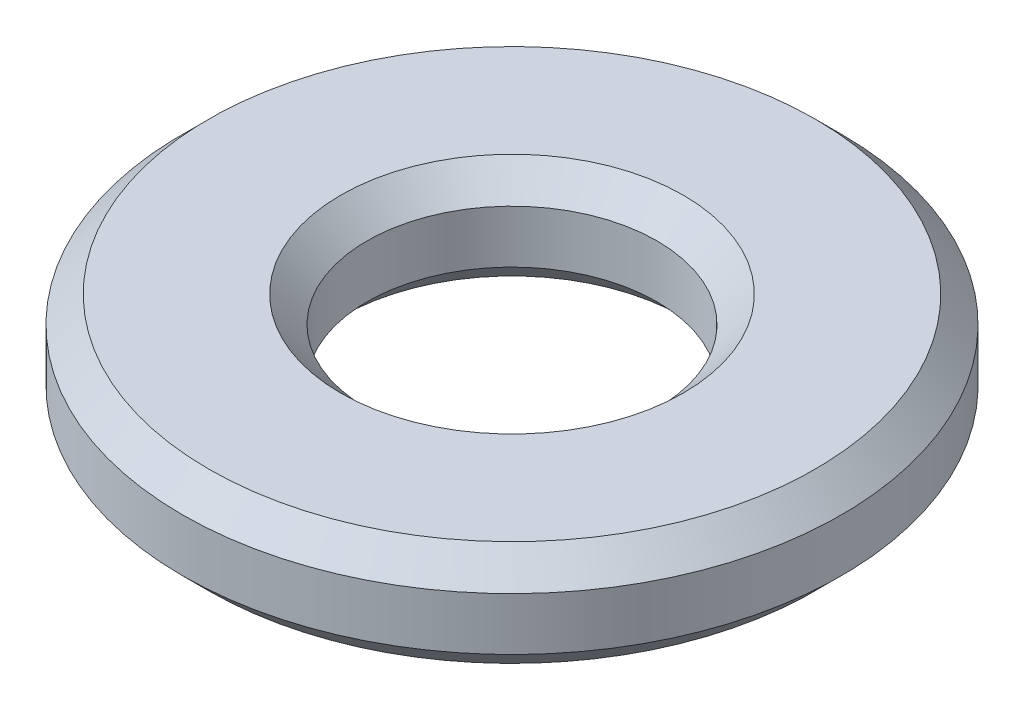
SolidWorks part; units mm, degrees
ref_plane "Alzado" through (0, 0, 0) normal (0, 0, 1) x (1, 0, 0)
ref_plane "Planta" through (0, 0, 0) normal (0, 1, 0) x (1, 0, 0)
ref_plane "Vista lateral" through (0, 0, 0) normal (1, 0, 0) x (0, 0, -1)
sketch "Croquis1" plane through (0, 0, 0) normal (0, 1, 0) x (1, 0, 0)
  circle A0 centre (0, 0) radius 1.1
  circle A1 centre (0, 0) radius 2.5
  dimension "D1" = 2.2
  dimension "D2" = 5
extrude "Saliente-Extruir1" add sketch "Croquis1" along normal blind 0.8
chamfer "Chaflán1" distance 0.2 angle 45 4 edges at (0, 0, 1.1) (0, 0, 2.5) (0, 0.8, 1.1) (0, 0.8, 2.5)
